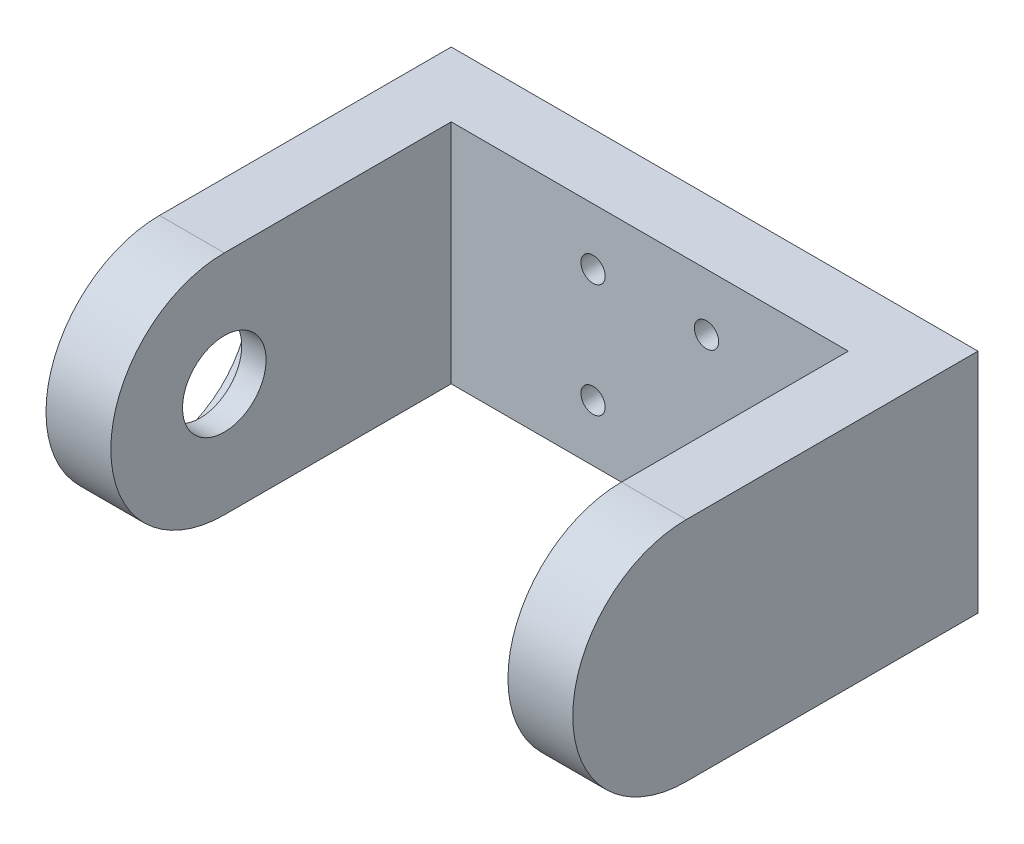
SolidWorks part; units mm, degrees
ref_plane "Alzado" through (0, 0, 0) normal (0, 0, 1) x (1, 0, 0)
ref_plane "Planta" through (0, 0, 0) normal (0, 1, 0) x (1, 0, 0)
ref_plane "Vista lateral" through (0, 0, 0) normal (1, 0, 0) x (0, 0, -1)
sketch "Croquis1" plane through (0, 0, 0) normal (0, 0, 1) x (1, 0, 0)
  line L1 (0, 0) -> (65, 0)
  line L2 (0, 0) -> (0, 28)
  line L3 (0, 28) -> (65, 28)
  line L4 (65, 0) -> (65, 28)
  dimension "D1" = 65
  dimension "D2" = 28
extrude "Saliente-Extruir1" add sketch "Croquis1" along normal blind 8
sketch "Croquis2" plane through (0, 0, 8) normal (0, 0, 1) x (1, 0, 0)
  line L0 (65, 28) -> (0, 28) construction
  line L1 (0, 0) -> (8, 0)
  line L2 (0, 0) -> (0, 28)
  line L3 (0, 28) -> (8, 28)
  line L4 (8, 0) -> (8, 28)
  line L6 (65, 0) -> (57, 0)
  line L7 (65, 0) -> (65, 28)
  line L8 (65, 28) -> (57, 28)
  line L9 (57, 0) -> (57, 28)
  dimension "D1" = 8
  dimension "D2" = 8
extrude "Saliente-Extruir2" add sketch "Croquis2" along normal blind 28
sketch "Croquis3" plane through (0, 0, 0) normal (-1, 0, 0) x (0, 0, 1)
  line L0 (36, 28) -> (36, 0) construction
  circle A0 centre (36, 14) radius 14
extrude "Saliente-Extruir3" add sketch "Croquis3" against normal blind 8
sketch "Croquis4" plane through (65, 0, 0) normal (1, 0, 0) x (0, 0, -1)
  line L0 (-36, 0) -> (-36, 28) construction
  circle A0 centre (-36, 14) radius 14
extrude "Saliente-Extruir4" add sketch "Croquis4" against normal blind 8
sketch "Croquis5" plane through (0, 0, 0) normal (-1, 0, 0) x (0, 0, 1)
  line L0 (36, 28) -> (36, 0) construction
  line L1 (36, 0) -> (0, 0) construction
  arc A0 (36, 0) -> (36, 28) centre (36, 14) ccw construction
  circle A1 centre (36, 14) radius 11.115
extrude "Cortar-Extruir1" cut sketch "Croquis5" against normal blind 5
sketch "Croquis6" plane through (0, 0, 0) normal (-1, 0, 0) x (0, 0, 1)
  line L0 (36, 28) -> (36, 0) construction
  line L1 (36, 28) -> (0, 28) construction
  arc A0 (36, 0) -> (36, 28) centre (36, 14) ccw construction
  circle A1 centre (36, 14) radius 5.155
extrude "Cortar-Extruir2" cut sketch "Croquis6" against normal blind 8
sketch "Croquis7" plane through (65, 0, 0) normal (1, 0, 0) x (0, 0, -1)
  line L0 (-36, 28) -> (-36, 0) construction
  arc A0 (-36, 28) -> (-36, 0) centre (-36, 14) ccw construction
  circle A1 centre (-36, 14) radius 6.5
extrude "Cortar-Extruir3" cut sketch "Croquis7" along normal blind 5 from surface at -8 starting at face at (57, 14, 25.5)
sketch "Croquis8" plane through (0, 0, 8) normal (0, 0, 1) x (1, 0, 0)
  line L0 (32.5, 28) -> (32.5, 0) construction
  line L1 (57, 28) -> (8, 28) construction
  line L2 (8, 0) -> (57, 0) construction
  line L3 (32.5, 28) -> (46.5, 28) construction
  line L4 (32.5, 28) -> (18.5, 28) construction
  line L5 (25.5, 28) -> (25.5, 0) construction
  line L6 (39.5, 28) -> (39.5, 0) construction
  line L7 (39.5, 14) -> (39.5, 28) construction
  line L8 (39.5, 21) -> (25.5, 21) construction
  line L9 (39.5, 14) -> (39.5, 0) construction
  line L10 (39.5, 7) -> (25.5, 7) construction
  circle A0 centre (39.5, 21) radius 1.5
  circle A1 centre (25.5, 21) radius 1.5
  circle A2 centre (25.5, 7) radius 1.5
  circle A3 centre (39.5, 7) radius 1.5
  dimension "D1" = 14
  dimension "D2" = 14
extrude "Cortar-Extruir4" cut sketch "Croquis8" against normal blind 8
